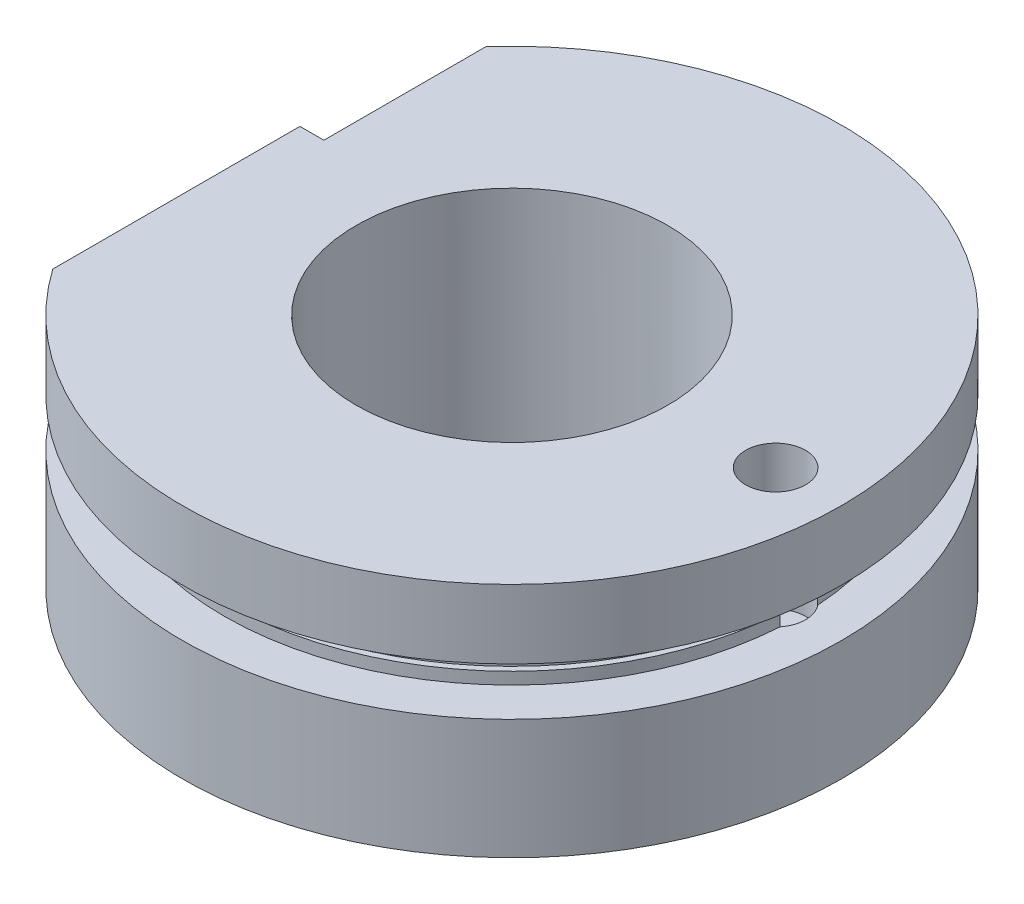
SolidWorks part; units mm, degrees
material "АЛ8Т4 ГОСТ 1583-93"
ref_plane "Спереди" through (0, 0, 0) normal (0, 0, 1) x (1, 0, 0)
ref_plane "Сверху" through (0, 0, 0) normal (0, 1, 0) x (1, 0, 0)
ref_plane "Справа" through (0, 0, 0) normal (1, 0, 0) x (0, 0, -1)
sketch "Эскиз1" plane through (0, 0, 0) normal (0, 1, 0) x (1, 0, 0)
  line L0 (-22.5, 15.8114) -> (-22.5, -15.8114)
  arc A0 (-22.5, -15.8114) -> (-22.5, 15.8114) centre (0, 0) ccw
  point P5 (27.5, 0)
  dimension "D1" = 55
  dimension "D2" = 50
extrude "Бобышка-Вытянуть1" add sketch "Эскиз1" along normal blind 19.75
sketch "Эскиз2" plane through (0, 0, 0) normal (0, 1, 0) x (1, 0, 0)
  circle A0 centre (0, 0) radius 13
  dimension "D1" = 26
extrude "Вырез-Вытянуть2" cut sketch "Эскиз2" along normal through all
sketch "Эскиз3" plane through (0, 0, 0) normal (1, 0, 0) x (0, 0, -1)
  line L0 (0, 0) -> (0, 19.75) construction
  line L1 (-29, 14) -> (-24, 14)
  line L2 (-29, 14) -> (-29, 10)
  line L3 (-29, 10) -> (-24, 10)
  line L4 (-24, 14) -> (-24, 13)
  line L5 (27.5, 19.75) -> (-27.5, 19.75) construction
  line L6 (-24, 13) -> (-23.5, 13)
  line L7 (-23.5, 13) -> (-23.5, 11)
  line L8 (-23.5, 11) -> (-24, 11)
  line L9 (-24, 11) -> (-24, 10)
  dimension "D1" = 10
  dimension "D2" = 4
  dimension "D3" = 24
  dimension "D4" = 5
  dimension "D5" = 23.5
  dimension "D6" = 1
  dimension "D7" = 1
revolve "Вырез-Повернуть1" cut sketch "Эскиз3" angle 360 about L0
sketch "Эскиз4" plane through (0, 0, 0) normal (0, 1, 0) x (1, 0, 0)
  circle A0 centre (13, 0) radius 1.5
  circle A1 centre (0, 0) radius 13 construction
  dimension "D1" = 3
ref_plane "Плоскость1" through (0, 0, -4.81) normal (0, 0, 1) x (1, 0, 0)
sketch "Эскиз5" plane through (0, 0, -4.81) normal (0, 0, 1) x (1, 0, 0)
  line L0 (-22.5, 19.75) -> (-20.5, 19.75)
  line L1 (27.5, 19.75) -> (-22.5, 19.75) construction
  line L2 (-20.5, 19.75) -> (-22.5, 17.75)
  line L3 (-22.5, 19.75) -> (-22.5, 14) construction
  line L4 (-22.5, 17.75) -> (-22.5, 19.75)
  dimension "D1" = 2
  dimension "D2" = 2
extrude "Вырез-Вытянуть4" cut sketch "Эскиз5" against normal through all
hole_wizard "Диаметр отверстия Ø5.0 (5)1" positions "Эскиз8" profile "Эскиз7" hole size "Ø5.0" standard "Din"
sketch "Эскиз8" plane through (0, 19.75, 0) normal (0, 1, 0) x (1, 0, 0)
  arc A0 (-22.5, -15.8114) -> (-22.5, 15.8114) centre (0, 0) ccw construction
  point P0 (22, 0)
  point P4 (27.5, 0)
  dimension "D1" = 5.5
sketch "Эскиз7" plane through (22, 19.75, 0) normal (1, 0, 0) x (0, 0, 1)
  line L0 (0, 0) -> (0, 12)
  line L1 (0, 12) -> (2.5, 12)
  line L2 (2.5, 12) -> (2.5, 0)
  line L5 (2.5, 0) -> (0, 0)
  line L10 (0, 12) -> (-2.5, 12) construction
  line L11 (0, -6.35) -> (0, 107.95) construction
  dimension "Диаметр отверстия" = 5
  dimension "Глубина отверстия" = 12
  dimension "Угол заточки сверла" = 180
sketch "Эскиз9" plane through (0, 0, 0) normal (0, 0, 1) x (1, 0, 0)
  circle A0 centre (0, 12) radius 1
  dimension "D1" = 2
  dimension "D2" = 12
extrude "Вырез-Вытянуть5" cut sketch "Эскиз9" along normal through all
sketch "Эскиз10" plane through (0, 0, 0) normal (0, 1, 0) x (1, 0, 0)
  circle A0 centre (0, 0) radius 13
  dimension "D1" = 26
curve "Спираль1" pitch 95 height 19 turns 0.2
sketch "Эскиз11" plane through (0, 0, 0) normal (0, 1, 0) x (1, 0, 0)
  circle A0 centre (0, 13) radius 1
  circle A1 centre (0, 0) radius 13 construction
  spline S0 degree 3 poles (0, 13) (1.8095, 13) (5.4472, 12.2278) (9.9461, 8.9592) (11.8046, 5.7382) (12.3637, 4.0172) knots 0 0 0 0 0.333333 0.666667 1 1 1 1 construction
  dimension "D1" = 2
sweep "Вырез-По траектории1" cut profiles "Эскиз11" path "Спираль1"
pattern_circular "Круговой массив1" count 2 every 17 about axis through (0, 19.75, 0) along (0, -1, 0) of "Вырез-По траектории1"
